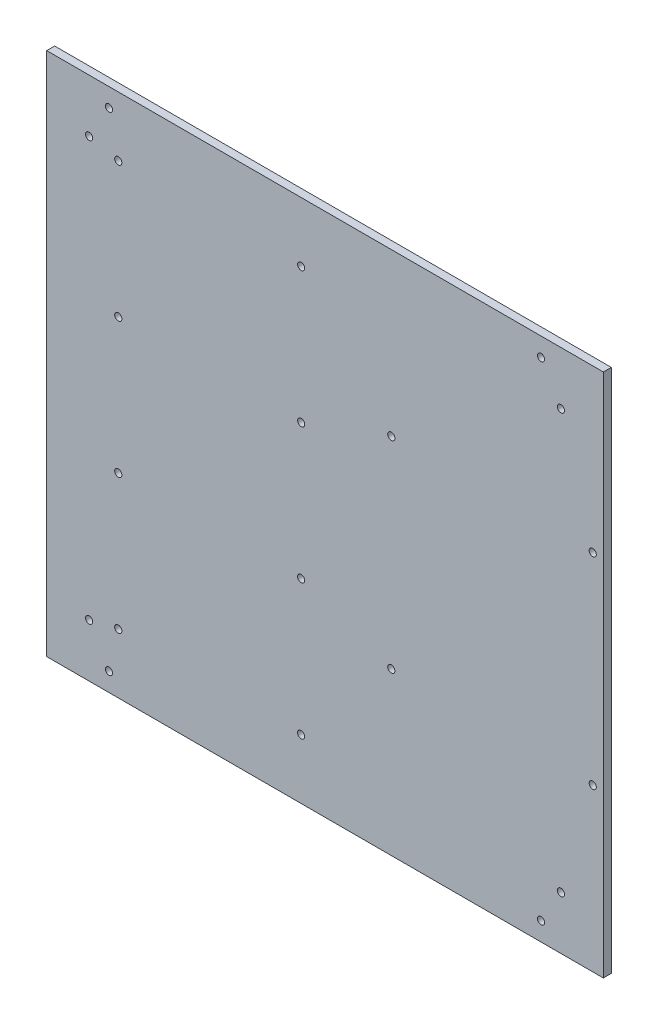
SolidWorks part; units mm, degrees
material "ABS"
ref_plane "Plan de face" through (0, 0, 0) normal (0, 0, 1) x (1, 0, 0)
ref_plane "Plan de dessus" through (0, 0, 0) normal (0, 1, 0) x (1, 0, 0)
ref_plane "Plan de droite" through (0, 0, 0) normal (1, 0, 0) x (0, 0, -1)
sketch "Esquisse1" plane through (0, 0, 0) normal (0, 0, 1) x (1, 0, 0)
  line L0 (-78, -25.5) -> (-9, -25.5) construction
  line L5 (-81.5, -92) -> (81.5, -92) construction
  line L6 (-81.5, -92) -> (-81.5, 92) construction
  line L7 (-81.5, 92) -> (81.5, 92) construction
  line L8 (81.5, -92) -> (81.5, 92) construction
  line L9 (-81.5, -92) -> (81.5, 92) construction
  line L10 (-81.5, 92) -> (81.5, -92) construction
  line L11 (-89, 79) -> (89, 79) construction
  line L12 (-89, 79) -> (-89, -79) construction
  line L13 (-89, -79) -> (89, -79) construction
  line L14 (89, 79) -> (89, -79) construction
  line L15 (-89, 79) -> (89, -79) construction
  line L16 (-89, -79) -> (89, 79) construction
  line L17 (-78, 76.5) -> (-9, 76.5) construction
  line L18 (-78, 76.5) -> (-78, 25.5) construction
  line L19 (-78, 25.5) -> (-9, 25.5) construction
  line L20 (-9, 76.5) -> (-9, 25.5) construction
  line L21 (-78, 76.5) -> (-9, 25.5) construction
  line L22 (-78, 25.5) -> (-9, 76.5) construction
  line L23 (-78, -25.5) -> (-78, -76.5) construction
  line L24 (-78, -76.5) -> (-9, -76.5) construction
  line L25 (-9, -25.5) -> (-9, -76.5) construction
  line L26 (-78, -25.5) -> (-9, -76.5) construction
  line L27 (-78, -76.5) -> (-9, -25.5) construction
  line L28 (-16.2686, 0) -> (12.6201, 0) construction
  line L29 (25, 38) -> (101, 38) construction
  line L30 (25, 38) -> (25, -38) construction
  line L31 (25, -38) -> (101, -38) construction
  line L32 (101, 38) -> (101, -38) construction
  line L33 (25, 38) -> (101, -38) construction
  line L34 (25, -38) -> (101, 38) construction
  line L36 (-105, 99) -> (105, 99)
  line L37 (-105, 99) -> (-105, -99)
  line L38 (-105, -99) -> (105, -99)
  line L39 (105, 99) -> (105, -99)
  line L40 (-105, 99) -> (105, -99) construction
  line L41 (-105, -99) -> (105, 99) construction
  point P0 (0, 0)
  point P7 (0, 0)
  point P12 (-43.5, 51)
  point P17 (-43.5, -51)
  point P22 (63, 0)
  point P29 (0, 0)
  dimension "D1" = 163
  dimension "D2" = 184
  dimension "D3" = 178
  dimension "D4" = 158
  dimension "D5" = 69
  dimension "D6" = 51
  dimension "D9" = 51
  dimension "D10" = 76
  dimension "D11" = 76
  dimension "D12" = 11
  dimension "D13" = 56.5
  dimension "D14" = 210
  dimension "D15" = 198
extrude "Boss.-Extru.1" add sketch "Esquisse1" along normal blind 3
hole_wizard "Dégagement M2.51" positions "Esquisse2" profile "Esquisse3" hole size "M2.5" standard "ISO" end condition up to next
sketch "Esquisse2" plane through (0, 0, 3) normal (0, 0, 1) x (1, 0, 0)
  point P0 (-81.5, -92)
  point P3 (-89, -79)
  point P6 (-78, -76.5)
  point P9 (-78, -25.5)
  point P12 (-9, -76.5)
  point P15 (-9, -25.5)
  point P18 (-9, 25.5)
  point P21 (-78, 25.5)
  point P24 (-78, 76.5)
  point P27 (-89, 79)
  point P30 (-81.5, 92)
  point P33 (25, 38)
  point P36 (25, -38)
  point P39 (101, -38)
  point P42 (101, 38)
  point P45 (89, 79)
  point P48 (81.5, 92)
  point P51 (81.5, -92)
  point P54 (89, -79)
  point P57 (-9, 76.5)
sketch "Esquisse3" plane through (-81.5, -92, 3) normal (1, 0, 0) x (0, -1, 0)
  line L0 (0, 0) -> (0, 3)
  line L1 (0, 3) -> (1.35, 3)
  line L2 (1.35, 3) -> (1.35, 0)
  line L5 (1.35, 0) -> (0, 0)
  line L11 (0, -6.35) -> (0, 107.95) construction
  dimension "Diamètre du perçage jusqu'au prochain" = 2.7
  dimension "Profondeur du perçage jusqu'au prochain" = 3
sketch "Esquisse4" plane through (0, 0, 3) normal (0, 0, 1) x (1, 0, 0)
  line L1 (-97.5, 139) -> (97.5, 139)
  line L2 (-97.5, 139) -> (-97.5, -139)
  line L3 (-97.5, -139) -> (97.5, -139)
  line L4 (97.5, 139) -> (97.5, -139)
  line L5 (-97.5, 139) -> (97.5, -139) construction
  line L6 (-97.5, -139) -> (97.5, 139) construction
  point P0 (0, 0)
  dimension "D1" = 195
  dimension "D2" = 278
